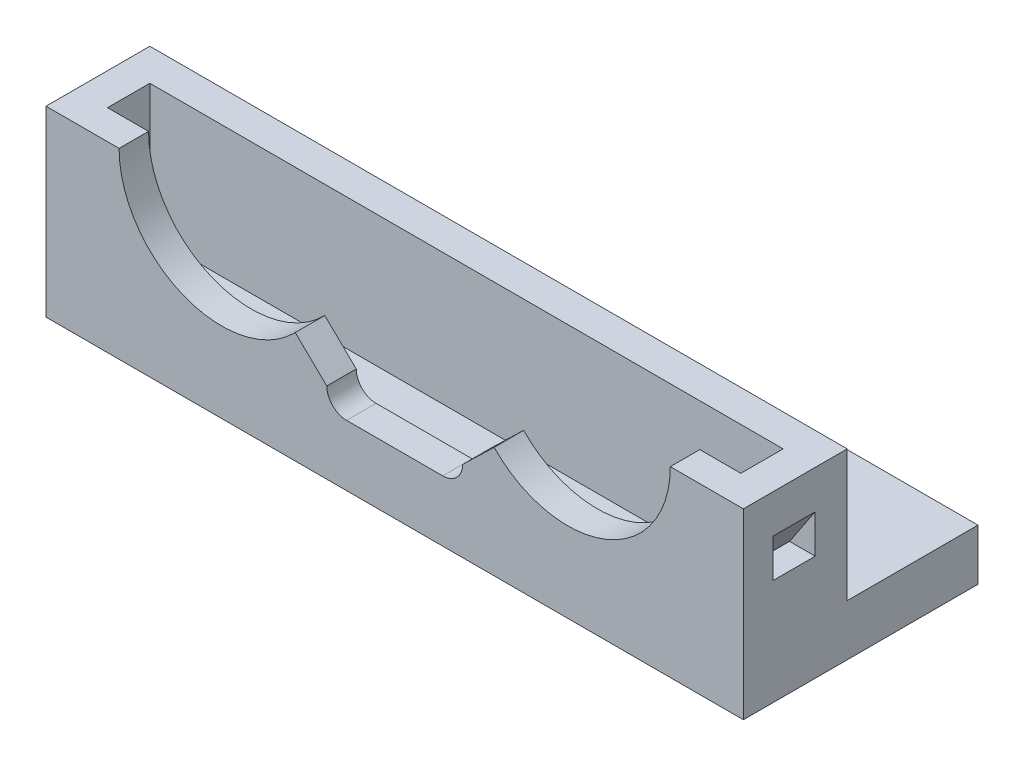
SolidWorks part; units mm, degrees
ref_plane "Front Plane" through (0, 0, 0) normal (0, 0, 1) x (1, 0, 0)
ref_plane "Top Plane" through (0, 0, 0) normal (0, 1, 0) x (1, 0, 0)
ref_plane "Right Plane" through (0, 0, 0) normal (1, 0, 0) x (0, 0, -1)
sketch "Sketch2" plane through (0, 0, 0) normal (0, 1, 0) x (1, 0, 0)
  line L1 (-27.2, -8) -> (27.2, -8)
  line L2 (-27.2, -8) -> (-27.2, 8)
  line L3 (-27.2, 8) -> (27.2, 8)
  line L4 (27.2, -8) -> (27.2, 8)
  line L5 (-27.2, -8) -> (27.2, 8) construction
  line L6 (-27.2, 8) -> (27.2, -8) construction
  point P0 (0, 0)
extrude "Boss-Extrude1" add sketch "Sketch2" along normal blind 4
sketch "Sketch3" plane through (27.2, 0, 0) normal (1, 0, 0) x (0, 0, -1)
  line L1 (-8, 0) -> (-10.3, 0)
  line L2 (-8, 0) -> (-8, 24)
  line L3 (-8, 24) -> (-10.3, 24)
  line L4 (-10.3, 0) -> (-10.3, 24)
extrude "Boss-Extrude2" add sketch "Sketch3" against normal blind 54.4
sketch "Sketch4" plane through (0, 4, 0) normal (0, 1, 0) x (1, 0, 0)
  line L0 (-27.2, 8) -> (-27.2, -8) construction
  line L1 (27.2, 8) -> (-27.2, 8) construction
  circle A0 centre (-13.5, 2.5) radius 2.3
  circle A1 centre (13.5, 2.5) radius 2.3
  dimension "D1" = 27
  dimension "D2" = 13.7
  dimension "D3" = 5.5
  dimension "D4" = 5.5
extrude "Cut-Extrude1" cut sketch "Sketch4" against normal blind 45
sketch "Sketch6" plane through (0, 0, 10.3) normal (0, 0, 1) x (1, 0, 0)
  line L0 (-3.75, 6.3) -> (3.75, 6.3) construction
  line L1 (-3.75, 7.85) -> (3.75, 7.85)
  line L2 (-3.75, 4.75) -> (3.75, 4.75)
  line L3 (-27.2, 0) -> (27.2, 0) construction
  arc A0 (-3.75, 7.85) -> (-3.75, 4.75) centre (-3.75, 6.3) ccw
  arc A1 (3.75, 4.75) -> (3.75, 7.85) centre (3.75, 6.3) ccw
  point P2 (0, 6.3)
  dimension "D3" = 1.55
  dimension "D1" = 4.75
  dimension "D2" = 7.5
extrude "Cut-Extrude3" cut sketch "Sketch6" against normal blind 10
sketch "Sketch5" plane through (0, 0, 10.3) normal (0, 0, 1) x (1, 0, 0)
  line L0 (-27.2, 0) -> (27.2, 0) construction
  line L1 (-27.2, 24) -> (-27.2, 0) construction
  circle A0 centre (-13.5, 14.25) radius 8
  circle A1 centre (13.5, 14.25) radius 8
  dimension "D1" = 14.25
  dimension "D2" = 27
  dimension "D3" = 14.25
  dimension "D4" = 13.7
extrude "Cut-Extrude2" cut sketch "Sketch5" against normal blind 10
sketch "Sketch7" plane through (0, 0, 10.3) normal (0, 0, 1) x (1, 0, 0)
  line L0 (-35.2427, 14.25) -> (-13.5, 14.25)
  line L1 (0, 6.5) -> (-5.3, 6.3)
  line L2 (-5.3, 6.3) -> (-13.5, 14.25)
  line L3 (0, 6.5) -> (5.3, 6.3)
  line L4 (13.5, 14.25) -> (21.5, 14.25)
  line L5 (-35.2427, 14.25) -> (-35.2427, 27.8876)
  line L6 (-35.2427, 27.8876) -> (36.0064, 27.8876)
  line L7 (5.3, 6.3) -> (13.5, 14.25)
  line L8 (36.0064, 14.25) -> (36.0064, 27.8876)
  line L9 (21.5, 14.25) -> (36.0064, 14.25)
  arc A0 (-3.75, 7.85) -> (-3.75, 4.75) centre (-3.75, 6.3) ccw construction
  arc A1 (3.75, 4.75) -> (3.75, 7.85) centre (3.75, 6.3) ccw construction
  circle A2 centre (13.5, 14.25) radius 8 construction
  point P10 (0, 6.5)
extrude "Cut-Extrude4" cut sketch "Sketch7" against normal blind 10
sketch "Sketch8" plane through (27.2, 0, 0) normal (1, 0, 0) x (0, 0, -1)
  line L0 (-8, 4) -> (8, 4) construction
  line L2 (-4.7, 14.25) -> (-2.2, 14.25)
  line L3 (-4.7, 14.25) -> (-4.7, 4)
  line L4 (-4.7, 4) -> (-2.2, 4)
  line L8 (-2.2, 14.25) -> (-2.2, 4)
  line L9 (-4.7, 14.25) -> (-2.2, 4) construction
  line L10 (-4.7, 4) -> (-2.2, 14.25) construction
  line L11 (-8, 4) -> (-8, 14.25) construction
  point P0 (-3.45, 9.125)
  dimension "D1" = 0
  dimension "D2" = 3.3
  dimension "D3" = 2.5
extrude "Boss-Extrude3" add sketch "Sketch8" against normal blind 54.4
sketch "Sketch9" plane through (0, 4, 0) normal (0, 1, 0) x (1, 0, 0)
  line L1 (-27.2, -4.7) -> (27.2, -4.7) construction
  line L2 (-27.2, -4.7) -> (-24.7, -4.7)
  line L3 (-27.2, -4.7) -> (-27.2, -8)
  line L4 (-27.2, -8) -> (-24.7, -8)
  line L5 (-24.7, -4.7) -> (-24.7, -8)
  line L6 (-27.2, -4.7) -> (-24.7, -8) construction
  line L7 (-27.2, -8) -> (-24.7, -4.7) construction
  line L8 (-27.2, -8) -> (27.2, -8) construction
  line L9 (-27.2, -4.7) -> (-27.2, -8) construction
  line L10 (-27.2, -4.7) -> (27.2, -4.7) construction
  line L11 (27.2, -4.7) -> (24.7, -4.7)
  line L12 (27.2, -4.7) -> (27.2, -8)
  line L13 (27.2, -8) -> (24.7, -8)
  line L14 (24.7, -4.7) -> (24.7, -8)
  line L15 (27.2, -4.7) -> (24.7, -8) construction
  line L16 (27.2, -8) -> (24.7, -4.7) construction
  line L17 (27.2, -8) -> (27.2, -4.7) construction
  point P0 (-25.95, -6.35)
  point P13 (25.95, -6.35)
  dimension "D1" = 0
  dimension "D2" = 0
  dimension "D3" = 0
  dimension "D4" = 2.5
  dimension "D5" = 0
  dimension "D6" = 0
  dimension "D7" = 0
  dimension "D8" = 2.5
extrude "Boss-Extrude4" add sketch "Sketch9" along normal blind 10.25
sketch "Sketch10" plane through (0, 0, 4.7) normal (0, 0, 1) x (1, 0, 0)
  line L0 (-27.2, 8.25) -> (-25.2, 8.25)
  line L1 (27.2, 14.25) -> (27.2, 0) construction
  line L3 (27.2, 11.25) -> (27.2, 8.25)
  line L5 (-27.2, 11.25) -> (-27.2, 8.25)
  line L6 (27.2, 8.25) -> (25.2, 8.25)
  line L7 (25.2, 8.25) -> (27.2, 11.25)
  line L8 (-25.2, 8.25) -> (-27.2, 11.25)
extrude "Cut-Extrude5" cut sketch "Sketch10" along normal blind 3.3
